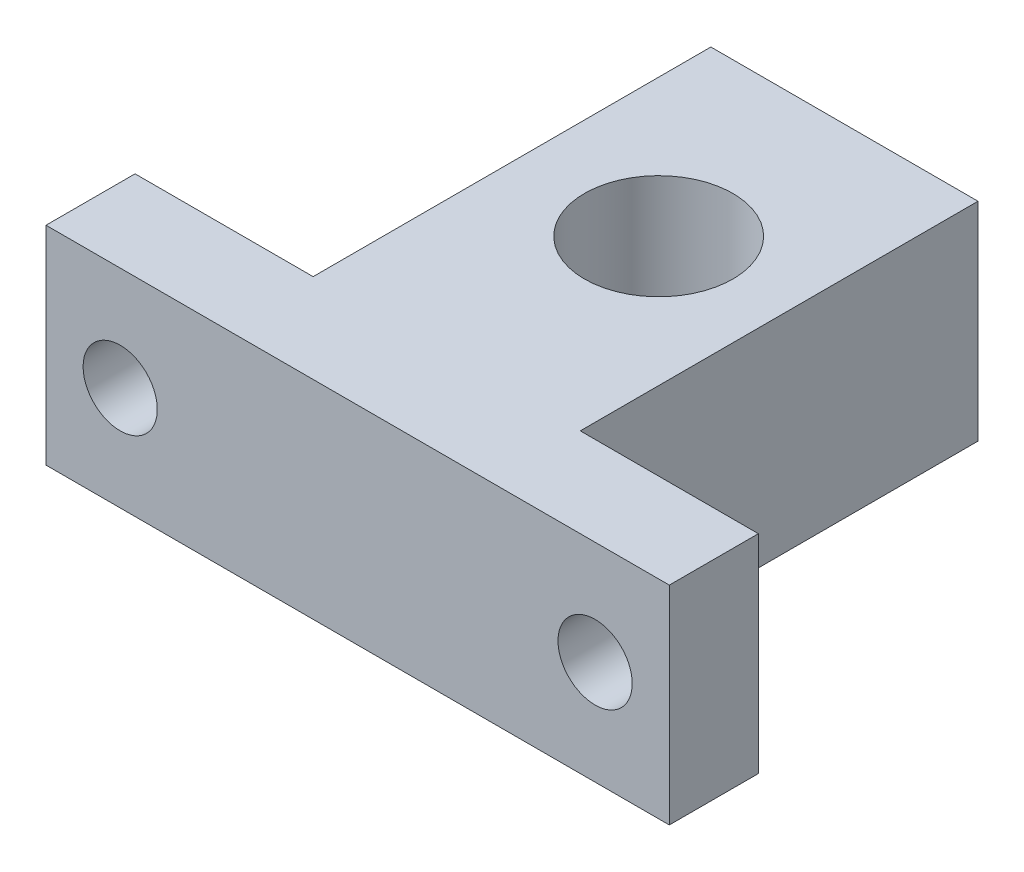
SolidWorks part; units mm, degrees
ref_plane "前视基准面" through (0, 0, 0) normal (0, 0, 1) x (1, 0, 0)
ref_plane "上视基准面" through (0, 0, 0) normal (0, 1, 0) x (1, 0, 0)
ref_plane "右视基准面" through (0, 0, 0) normal (1, 0, 0) x (0, 0, -1)
sketch "草图1" plane through (0, 0, 0) normal (0, 1, 0) x (1, 0, 0)
  line L1 (-9.2842, 14.4474) -> (8.7158, 14.4474)
  line L2 (-9.2842, 14.4474) -> (-9.2842, -12.3526)
  line L4 (8.7158, 14.4474) -> (8.7158, -12.3526)
  line L5 (-0.2842, -18.3526) -> (20.7158, -18.3526)
  line L7 (8.7158, -12.3526) -> (20.7158, -12.3526)
  line L8 (20.7158, -18.3526) -> (20.7158, -12.3526)
  line L9 (-0.2842, -18.3526) -> (-21.2842, -18.3526)
  line L11 (-9.2842, -12.3526) -> (-21.2842, -12.3526)
  line L12 (-21.2842, -18.3526) -> (-21.2842, -12.3526)
  circle A0 centre (0, 1.6474) radius 5
  dimension "D5" = 20
  dimension "D1" = 18
  dimension "D2" = 32.8
  dimension "D3" = 6
  dimension "D4" = 42
extrude "凸台-拉伸1" add sketch "草图1" along normal blind 14
sketch "草图2" plane through (0, 0, 12.3526) normal (0, 0, -1) x (-1, 0, 0)
  line L0 (-20.7158, 7) -> (21.2842, 7) construction
  line L1 (-20.7158, 14) -> (-20.7158, 0) construction
  line L2 (21.2842, 14) -> (21.2842, 0) construction
  circle A0 centre (-15.7158, 7) radius 2.5
  circle A1 centre (16.2842, 7) radius 2.5
  dimension "D1" = 5
  dimension "D2" = 5
extrude "切除-拉伸1" cut sketch "草图2" against normal blind 14
